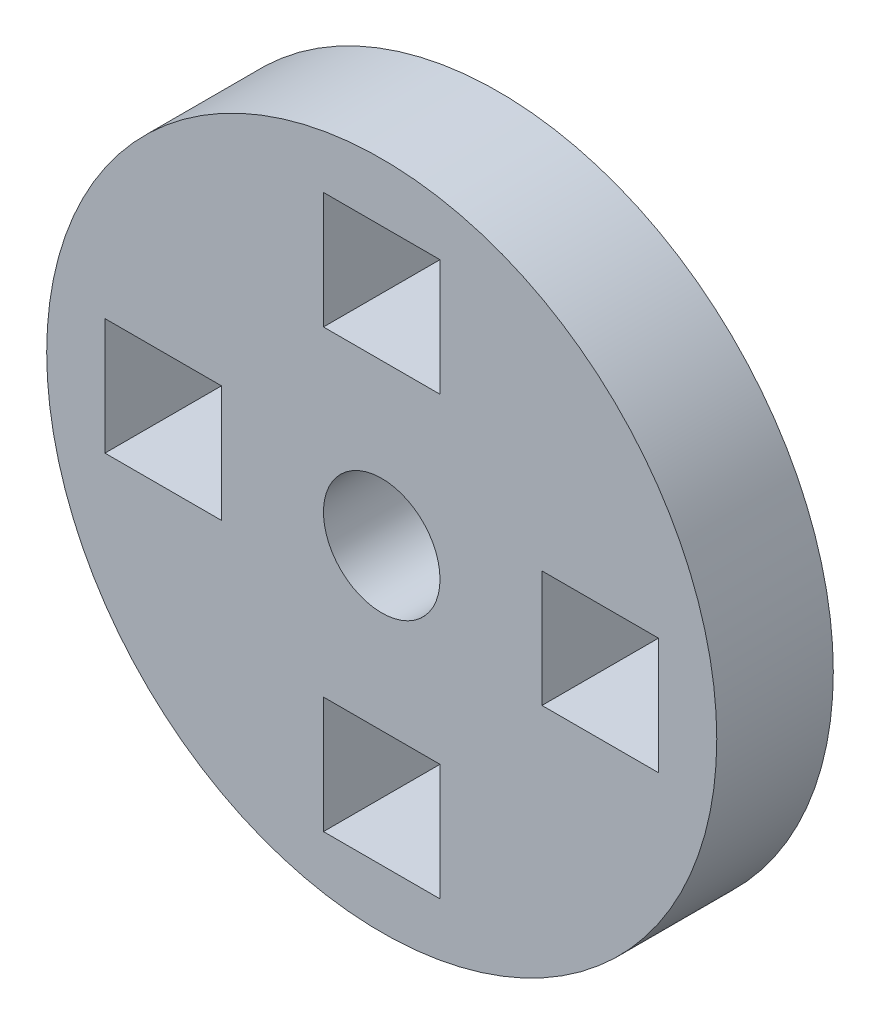
SolidWorks part; units mm, degrees
ref_plane "Front Plane" through (0, 0, 0) normal (0, 0, 1) x (1, 0, 0)
ref_plane "Top Plane" through (0, 0, 0) normal (0, 1, 0) x (1, 0, 0)
ref_plane "Right Plane" through (0, 0, 0) normal (1, 0, 0) x (0, 0, -1)
sketch "Sketch1" plane through (0, 0, 0) normal (0, 0, 1) x (1, 0, 0)
  line L0 (0, 5.5) -> (0, 0) construction
  line L1 (-2, 9.5) -> (2, 9.5)
  line L2 (-2, 9.5) -> (-2, 5.5)
  line L3 (-2, 5.5) -> (2, 5.5)
  line L4 (2, 9.5) -> (2, 5.5)
  line L5 (0, 0) -> (0, -5.5) construction
  line L6 (9.5, 2) -> (5.5, 2)
  line L7 (-2, -5.5) -> (2, -5.5)
  line L8 (-2, -5.5) -> (-2, -9.5)
  line L9 (-2, -9.5) -> (2, -9.5)
  line L10 (2, -5.5) -> (2, -9.5)
  line L11 (9.5, 2) -> (9.5, -2)
  line L12 (9.5, -2) -> (5.5, -2)
  line L13 (5.5, 2) -> (5.5, -2)
  line L14 (-5.5, 2) -> (-9.5, 2)
  line L15 (-5.5, 2) -> (-5.5, -2)
  line L16 (-5.5, -2) -> (-9.5, -2)
  line L17 (-9.5, 2) -> (-9.5, -2)
  circle A0 centre (0, 0) radius 11.5
  point P23 (0, 0)
  dimension "D1" = 23
  dimension "D2" = 4
  dimension "D3" = 11
  dimension "D4" = 2
extrude "Boss-Extrude1" add sketch "Sketch1" along normal blind 4
sketch "Sketch2" plane through (0, 0, 4) normal (0, 0, 1) x (1, 0, 0)
  circle A0 centre (0, 0) radius 2
  dimension "D1" = 4
extrude "Cut-Extrude1" cut sketch "Sketch2" against normal blind 4
